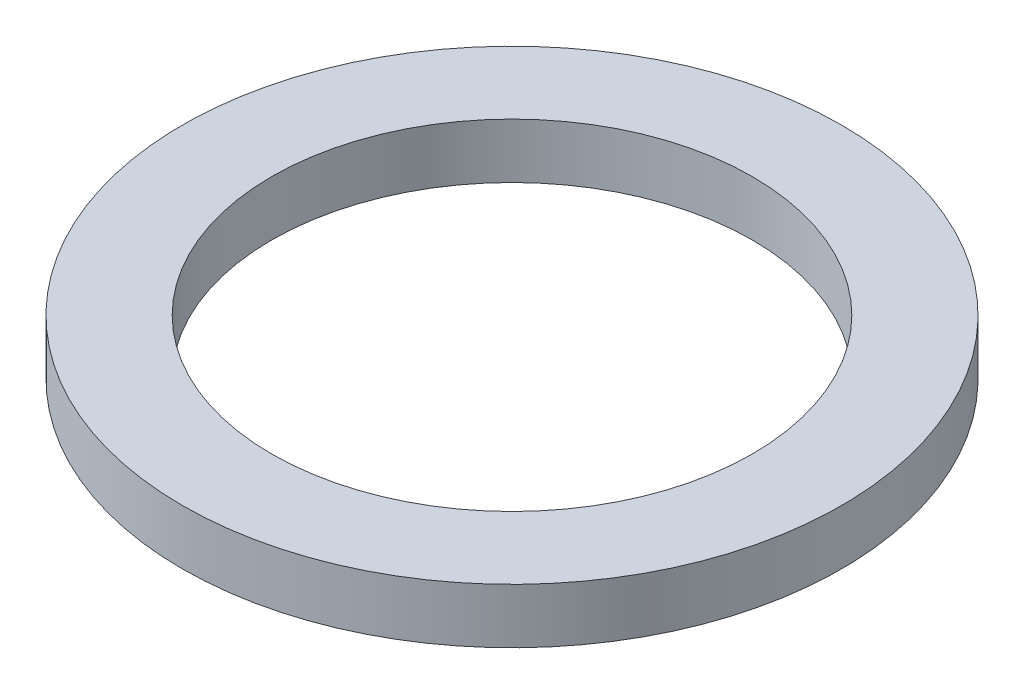
SolidWorks part; units mm, degrees
ref_plane "Front Plane" through (0, 0, 0) normal (0, 0, 1) x (1, 0, 0)
ref_plane "Top Plane" through (0, 0, 0) normal (0, 1, 0) x (1, 0, 0)
ref_plane "Right Plane" through (0, 0, 0) normal (1, 0, 0) x (0, 0, -1)
sketch "Sketch1" plane through (0, 0, 0) normal (0, 1, 0) x (1, 0, 0)
  circle A0 centre (0, 0) radius 76.2
  circle A1 centre (0, 0) radius 55.5625
  dimension "D1" = 152.4
  dimension "D2" = 111.125
extrude "Boss-Extrude1" add sketch "Sketch1" along normal blind 12.7
